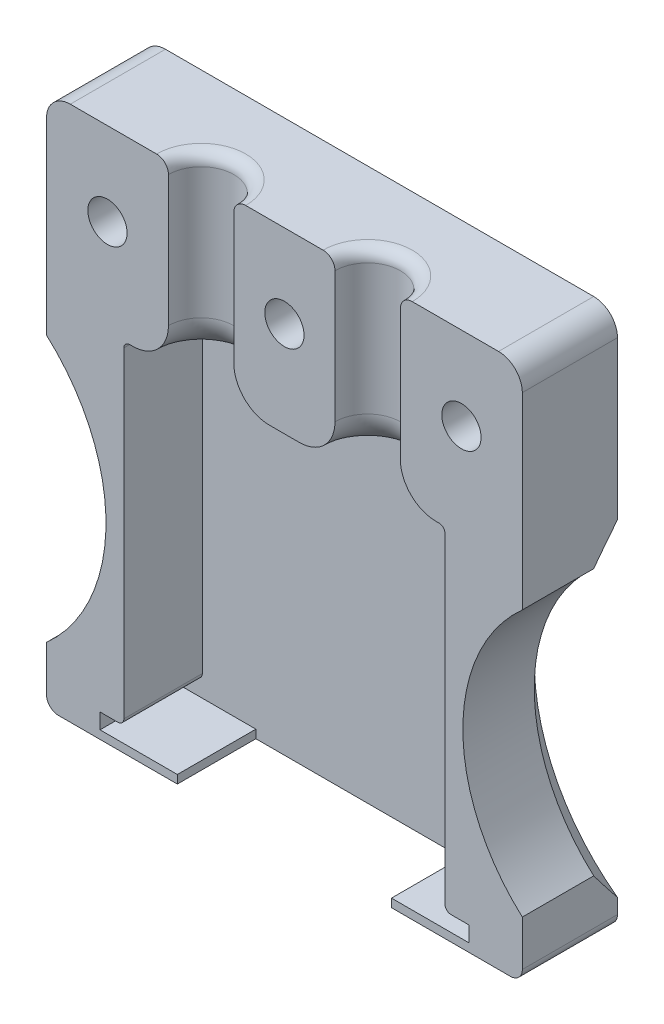
SolidWorks part; units mm, degrees
ref_plane "Alzado" through (0, 0, 0) normal (0, 0, 1) x (1, 0, 0)
ref_plane "Planta" through (0, 0, 0) normal (0, 1, 0) x (1, 0, 0)
ref_plane "Vista lateral" through (0, 0, 0) normal (1, 0, 0) x (0, 0, -1)
sketch "Croquis1" plane through (0, 0, 0) normal (0, 0, 1) x (1, 0, 0)
  line L1 (20, -22.5) -> (-20, -22.5)
  line L2 (20, -22.5) -> (20, 22.5)
  line L3 (20, 22.5) -> (-20, 22.5)
  line L4 (-20, -22.5) -> (-20, 22.5)
  line L5 (20, -22.5) -> (-20, 22.5) construction
  line L6 (20, 22.5) -> (-20, -22.5) construction
  point P0 (0, 0)
  dimension "D1" = 40
  dimension "D2" = 45
extrude "Saliente-Extruir1" add sketch "Croquis1" along normal blind 8
sketch "Croquis2" plane through (0, 0, 8) normal (0, 0, 1) x (1, 0, 0)
  line L0 (-20, -22.5) -> (20, -22.5) construction
  line L1 (15.5, -21.8) -> (-15.5, -21.8)
  line L2 (15.5, -21.8) -> (15.5, -20.5)
  line L3 (15.5, -20.5) -> (-15.5, -20.5)
  line L4 (-15.5, -21.8) -> (-15.5, -20.5)
  line L5 (15.5, -21.8) -> (-15.5, -20.5) construction
  line L6 (15.5, -20.5) -> (-15.5, -21.8) construction
  point P0 (0, -21.15)
  point P5 (0, 0)
  point P9 (0, -22.5)
  dimension "D1" = 1.3
  dimension "D2" = 0.7
  dimension "D3" = 31
extrude "Cortar-Extruir1" cut sketch "Croquis2" against normal blind 6.6
sketch "Croquis3" plane through (0, 0, 8) normal (0, 0, 1) x (1, 0, 0)
  line L0 (-20, 22.5) -> (-20, -22.5) construction
  circle A0 centre (-30, -6.5) radius 15
  circle A1 centre (30, -6.5) radius 15
  dimension "D1" = 30
  dimension "D6" = 30
  dimension "D2" = 10
  dimension "D3" = 16
  dimension "D4" = 16
  dimension "D5" = 10
extrude "Cortar-Extruir2" cut sketch "Croquis3" against normal blind 10
chamfer "Chaflán1" distance 2 angle 45 2 edges at (15, -6.5, 0) (-15, -6.5, 0)
sketch "Croquis4" plane through (0, 0, 8) normal (0, 0, 1) x (1, 0, 0)
  line L0 (-13.5, -20.5) -> (-13.5, 7.5)
  line L1 (15.5, -20.5) -> (-15.5, -20.5) construction
  line L2 (-13.5, 7.5) -> (13.5, 7.5)
  line L3 (13.5, 7.5) -> (13.5, -20.5)
  line L4 (13.5, -20.5) -> (-13.5, -20.5)
  dimension "D1" = 2
  dimension "D2" = 2
  dimension "D3" = 28
extrude "Cortar-Extruir3" cut sketch "Croquis4" against normal blind 6.6
sketch "Croquis6" plane through (0, 22.5, 0) normal (0, 1, 0) x (1, 0, 0)
  line L0 (20, -8) -> (-20, -8) construction
  circle A0 centre (7, -8) radius 2.75
  circle A1 centre (-7, -8) radius 2.75
  dimension "D1" = 5.5
  dimension "D2" = 5.5
  dimension "D3" = 13
  dimension "D4" = 13
extrude "Cortar-Extruir4" cut sketch "Croquis6" against normal blind 16.6
sketch "Croquis7" plane through (0, 0, 8) normal (0, 0, 1) x (1, 0, 0)
  circle A0 centre (0, 15.5) radius 1.65
  circle A1 centre (14.88, 15.5) radius 1.65
  circle A2 centre (-14.875, 15.5) radius 1.65
  dimension "D1" = 3.3
  dimension "D2" = 3.3
  dimension "D3" = 3.3
  dimension "D4" = 7
  dimension "D5" = 7
  dimension "D6" = 7
  dimension "D7" = 5.125
  dimension "D8" = 5.13
extrude "Cortar-Extruir5" cut sketch "Croquis7" against normal blind 16.6
sketch "Croquis8" plane through (0, 0, 0) normal (0, 0, -1) x (-1, 0, 0)
  circle A0 centre (14.875, 15.5) radius 4
  circle A1 centre (0, 15.5) radius 4
  circle A2 centre (-14.88, 15.5) radius 4
  dimension "D1" = 8
  dimension "D2" = 8
  dimension "D3" = 8
extrude "Cortar-Extruir6" cut sketch "Croquis8" against normal blind 4
sketch "Croquis9" plane through (0, -22.5, 0) normal (0, -1, 0) x (-1, 0, 0)
  line L0 (9, -8) -> (9, -1.4)
  line L1 (20, -8) -> (-20, -8) construction
  line L2 (9, -1.4) -> (-9, -1.4)
  line L3 (-9, -1.4) -> (-9, -8)
  line L4 (-9, -8) -> (9, -8)
  dimension "D1" = 18
  dimension "D2" = 11
  dimension "D3" = 11
  dimension "D4" = 6.6
extrude "Cortar-Extruir7" cut sketch "Croquis9" against normal blind 4
fillet "Redondeo1" radius 1 2 edges at (7, 22.5, 5.25) (-7, 22.5, 5.25)
fillet "Redondeo2" radius 2 2 edges at (20, 22.5, 4) (-20, 22.5, 4)
fillet "Redondeo3" radius 1 2 edges at (20, -22.5, 4) (-20, -22.5, 4)
fillet "Redondeo4" radius 3 2 edges at (7, 7.5, 5.25) (-7, 7.5, 5.25)
fillet "Redondeo5" radius 0.5 2 edges at (-13.5, -20.5, 4.7) (13.5, -20.5, 4.7)
fillet "Redondeo6" radius 0.5 2 edges at (13.5, 7.5, 4.7) (-13.5, 7.5, 4.7)
